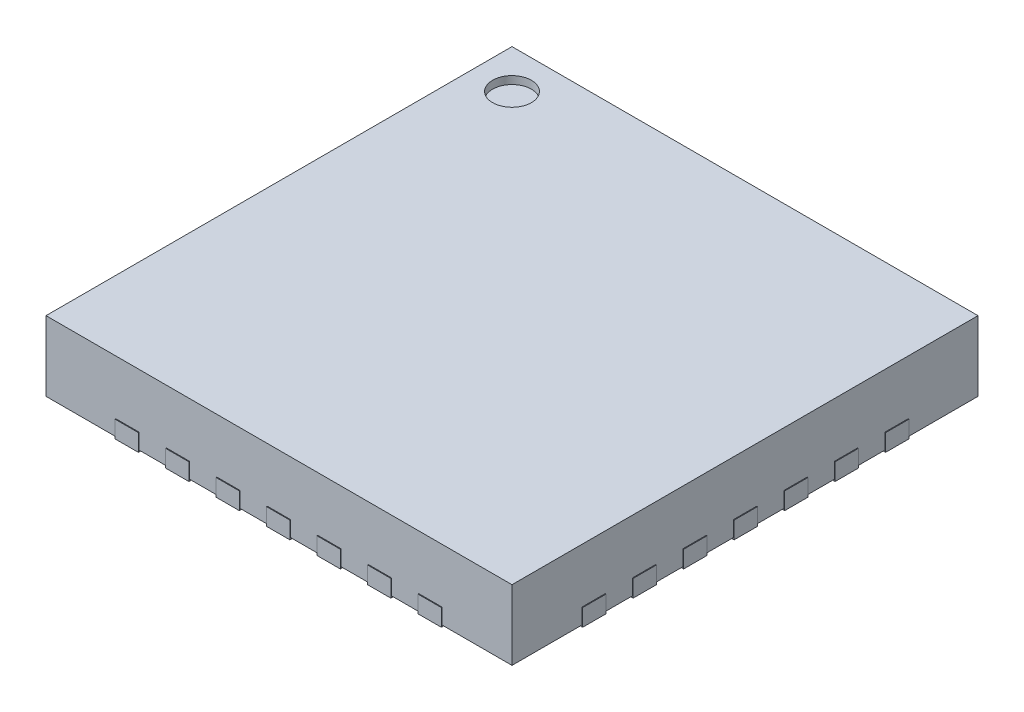
SolidWorks part; units mm, degrees
ref_plane "Front Plane" through (0, 0, 0) normal (0, 0, 1) x (1, 0, 0)
ref_plane "Top Plane" through (0, 0, 0) normal (0, 1, 0) x (1, 0, 0)
ref_plane "Right Plane" through (0, 0, 0) normal (1, 0, 0) x (0, 0, -1)
sketch "Sketch2" plane through (0, 0, 0) normal (0, 1, 0) x (1, 0, 0)
  line L1 (-3, -3) -> (3, -3)
  line L2 (-3, -3) -> (-3, 3)
  line L3 (-3, 3) -> (3, 3)
  line L4 (3, -3) -> (3, 3)
  line L5 (-3, -3) -> (3, 3) construction
  line L6 (-3, 3) -> (3, -3) construction
  point P0 (0, 0)
  dimension "D1" = 6
  dimension "D2" = 6
extrude "Boss-Extrude1" add sketch "Sketch2" along normal blind 0.9
sketch "Sketch3" plane through (0, 0, 0) normal (0, -1, 0) x (1, 0, 0)
  line L0 (-2.61, 0.5) -> (-2.61, 0.8)
  line L1 (-2.4, -2.4) -> (2.4, -2.4)
  line L2 (-2.4, -2.4) -> (-2.4, 2.4)
  line L3 (-2.4, 2.4) -> (2.4, 2.4)
  line L4 (2.4, -2.4) -> (2.4, 2.4)
  line L5 (-2.4, -2.4) -> (2.4, 2.4) construction
  line L6 (-2.4, 2.4) -> (2.4, -2.4) construction
  line L11 (-2.61, 0.5) -> (-3.01, 0.5)
  line L16 (3, 0) -> (-3, 0) construction
  line L17 (3, 3) -> (3, -3) construction
  line L18 (-3, -3) -> (-3, 3) construction
  line L19 (0, 3) -> (0, -3) construction
  line L20 (-3, 3) -> (3, 3) construction
  line L21 (3, -3) -> (-3, -3) construction
  line L23 (-2.61, -0.15) -> (-3.01, -0.15)
  line L24 (-2.61, -0.15) -> (-2.61, 0.15)
  line L25 (-2.61, 0.15) -> (-3.01, 0.15)
  line L26 (-3.01, -0.15) -> (-3.01, 0.15)
  line L27 (-2.61, -0.15) -> (-3.01, 0.15) construction
  line L28 (-2.61, 0.15) -> (-3.01, -0.15) construction
  line L80 (-3.01, 0.5) -> (-3.01, 0.8)
  line L81 (-2.61, 0.8) -> (-3.01, 0.8)
  line L110 (-2.61, 1.15) -> (-2.61, 1.45)
  line L111 (-2.61, 1.15) -> (-3.01, 1.15)
  line L140 (-3.01, 1.15) -> (-3.01, 1.45)
  line L141 (-2.61, 1.45) -> (-3.01, 1.45)
  line L142 (-2.61, 1.8) -> (-2.61, 2.1)
  line L143 (-2.61, 1.8) -> (-3.01, 1.8)
  line L144 (-3.01, 1.8) -> (-3.01, 2.1)
  line L145 (-2.61, 2.1) -> (-3.01, 2.1)
  line L146 (-2.61, -2.1) -> (-3.01, -2.1)
  line L147 (-3.01, -1.8) -> (-3.01, -2.1)
  line L148 (-2.61, -1.8) -> (-3.01, -1.8)
  line L149 (-2.61, -1.8) -> (-2.61, -2.1)
  line L150 (-2.61, -1.45) -> (-3.01, -1.45)
  line L151 (-3.01, -1.15) -> (-3.01, -1.45)
  line L152 (-2.61, -1.15) -> (-3.01, -1.15)
  line L153 (-2.61, -1.15) -> (-2.61, -1.45)
  line L154 (-2.61, -0.8) -> (-3.01, -0.8)
  line L155 (-3.01, -0.5) -> (-3.01, -0.8)
  line L156 (-2.61, -0.5) -> (-3.01, -0.5)
  line L157 (-2.61, -0.5) -> (-2.61, -0.8)
  line L158 (1.8, 2.61) -> (2.1, 2.61)
  line L159 (2.1, 2.61) -> (2.1, 3.01)
  line L160 (1.8, 3.01) -> (2.1, 3.01)
  line L161 (1.8, 2.61) -> (1.8, 3.01)
  line L162 (1.15, 2.61) -> (1.45, 2.61)
  line L163 (1.45, 2.61) -> (1.45, 3.01)
  line L164 (1.15, 3.01) -> (1.45, 3.01)
  line L165 (1.15, 2.61) -> (1.15, 3.01)
  line L166 (0.5, 2.61) -> (0.8, 2.61)
  line L167 (0.8, 2.61) -> (0.8, 3.01)
  line L168 (0.5, 3.01) -> (0.8, 3.01)
  line L169 (0.5, 2.61) -> (0.5, 3.01)
  line L170 (-0.15, 2.61) -> (0.15, 2.61)
  line L171 (-0.15, 2.61) -> (-0.15, 3.01)
  line L172 (-0.15, 3.01) -> (0.15, 3.01)
  line L173 (0.15, 2.61) -> (0.15, 3.01)
  line L174 (-0.8, 2.61) -> (-0.8, 3.01)
  line L175 (-0.5, 3.01) -> (-0.8, 3.01)
  line L176 (-0.5, 2.61) -> (-0.5, 3.01)
  line L177 (-0.5, 2.61) -> (-0.8, 2.61)
  line L178 (-1.45, 2.61) -> (-1.45, 3.01)
  line L179 (-1.15, 3.01) -> (-1.45, 3.01)
  line L180 (-1.15, 2.61) -> (-1.15, 3.01)
  line L181 (-1.15, 2.61) -> (-1.45, 2.61)
  line L182 (-2.1, 2.61) -> (-2.1, 3.01)
  line L183 (-1.8, 3.01) -> (-2.1, 3.01)
  line L184 (-1.8, 2.61) -> (-1.8, 3.01)
  line L185 (-1.8, 2.61) -> (-2.1, 2.61)
  line L186 (2.61, -1.8) -> (2.61, -2.1)
  line L187 (2.61, -2.1) -> (3.01, -2.1)
  line L188 (3.01, -1.8) -> (3.01, -2.1)
  line L189 (2.61, -1.8) -> (3.01, -1.8)
  line L190 (2.61, -1.15) -> (2.61, -1.45)
  line L191 (2.61, -1.45) -> (3.01, -1.45)
  line L192 (3.01, -1.15) -> (3.01, -1.45)
  line L193 (2.61, -1.15) -> (3.01, -1.15)
  line L194 (2.61, -0.5) -> (2.61, -0.8)
  line L195 (2.61, -0.8) -> (3.01, -0.8)
  line L196 (3.01, -0.5) -> (3.01, -0.8)
  line L197 (2.61, -0.5) -> (3.01, -0.5)
  line L198 (2.61, 0.15) -> (2.61, -0.15)
  line L199 (2.61, 0.15) -> (3.01, 0.15)
  line L200 (3.01, 0.15) -> (3.01, -0.15)
  line L201 (2.61, -0.15) -> (3.01, -0.15)
  line L202 (2.61, 0.8) -> (3.01, 0.8)
  line L203 (3.01, 0.5) -> (3.01, 0.8)
  line L204 (2.61, 0.5) -> (3.01, 0.5)
  line L205 (2.61, 0.5) -> (2.61, 0.8)
  line L206 (2.61, 1.45) -> (3.01, 1.45)
  line L207 (3.01, 1.15) -> (3.01, 1.45)
  line L208 (2.61, 1.15) -> (3.01, 1.15)
  line L209 (2.61, 1.15) -> (2.61, 1.45)
  line L210 (2.61, 2.1) -> (3.01, 2.1)
  line L211 (3.01, 1.8) -> (3.01, 2.1)
  line L212 (2.61, 1.8) -> (3.01, 1.8)
  line L213 (2.61, 1.8) -> (2.61, 2.1)
  line L214 (-1.8, -2.61) -> (-2.1, -2.61)
  line L215 (-2.1, -2.61) -> (-2.1, -3.01)
  line L216 (-1.8, -3.01) -> (-2.1, -3.01)
  line L217 (-1.8, -2.61) -> (-1.8, -3.01)
  line L218 (-1.15, -2.61) -> (-1.45, -2.61)
  line L219 (-1.45, -2.61) -> (-1.45, -3.01)
  line L220 (-1.15, -3.01) -> (-1.45, -3.01)
  line L221 (-1.15, -2.61) -> (-1.15, -3.01)
  line L222 (-0.5, -2.61) -> (-0.8, -2.61)
  line L223 (-0.8, -2.61) -> (-0.8, -3.01)
  line L224 (-0.5, -3.01) -> (-0.8, -3.01)
  line L225 (-0.5, -2.61) -> (-0.5, -3.01)
  line L226 (0.15, -2.61) -> (-0.15, -2.61)
  line L227 (0.15, -2.61) -> (0.15, -3.01)
  line L228 (0.15, -3.01) -> (-0.15, -3.01)
  line L229 (-0.15, -2.61) -> (-0.15, -3.01)
  line L230 (0.8, -2.61) -> (0.8, -3.01)
  line L231 (0.5, -3.01) -> (0.8, -3.01)
  line L232 (0.5, -2.61) -> (0.5, -3.01)
  line L233 (0.5, -2.61) -> (0.8, -2.61)
  line L234 (1.45, -2.61) -> (1.45, -3.01)
  line L235 (1.15, -3.01) -> (1.45, -3.01)
  line L236 (1.15, -2.61) -> (1.15, -3.01)
  line L237 (1.15, -2.61) -> (1.45, -2.61)
  line L238 (2.1, -2.61) -> (2.1, -3.01)
  line L239 (1.8, -3.01) -> (2.1, -3.01)
  line L240 (1.8, -2.61) -> (1.8, -3.01)
  line L241 (1.8, -2.61) -> (2.1, -2.61)
  point P0 (0, 0)
  point P18 (-2.81, 0)
  point P134 (0, 0)
  dimension "D1" = 4.8
  dimension "D2" = 4.8
  dimension "D3" = 0.01
  dimension "D4" = 0.4
  dimension "D5" = 0.3
  dimension "D7" = 0.35
  dimension "D9" = 0.3
  dimension "D10" = 0.21
  dimension "D6" = 4
  dimension "D8" = 4
extrude "Boss-Extrude2" add sketch "Sketch3" along normal blind 0.02 and the other way blind 0.2 separate body
sketch "Sketch4" plane through (0, 0.9, 0) normal (0, 1, 0) x (1, 0, 0)
  line L0 (3, 3) -> (-3, 3) construction
  line L1 (-3, 3) -> (-3, -3) construction
  circle A0 centre (-2.5, 2.5) radius 0.25
  dimension "D1" = 0.5
  dimension "D2" = 0.5
  dimension "D3" = 0.5
extrude "Cut-Extrude1" cut sketch "Sketch4" against normal blind 0.1
